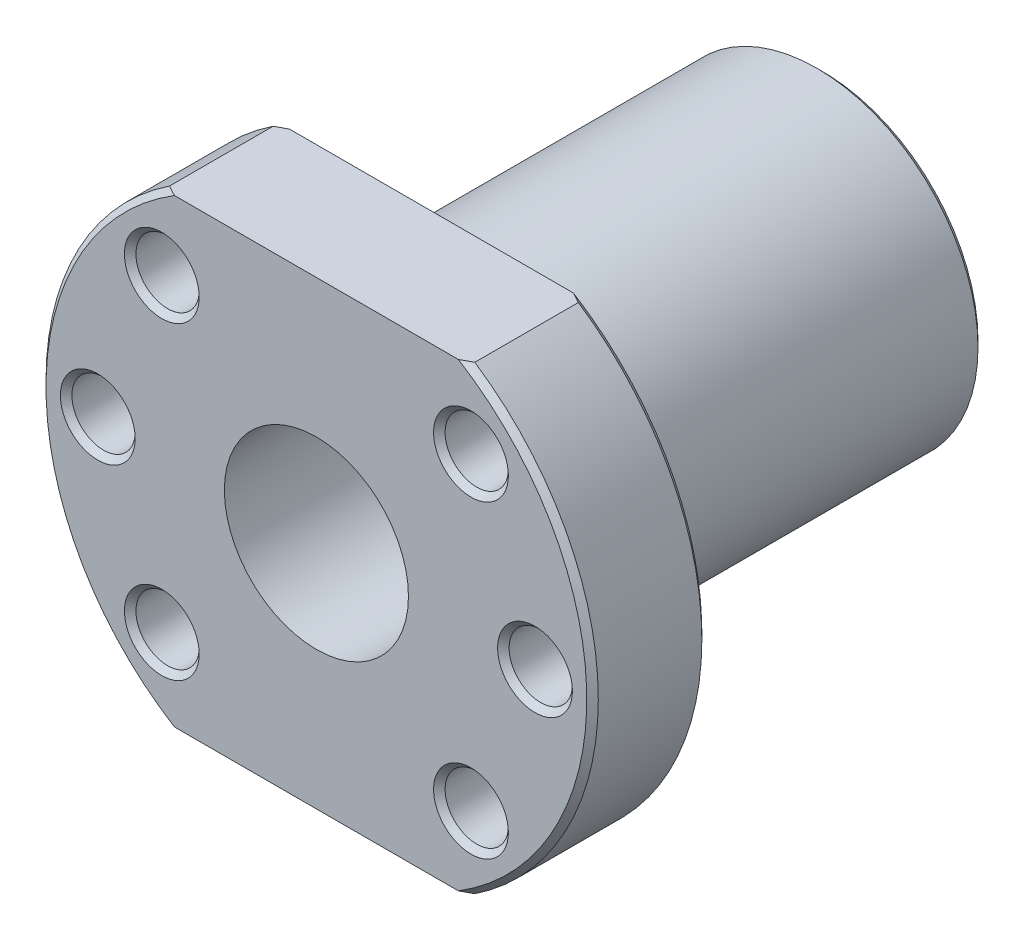
SolidWorks part; units mm, degrees
ref_plane "Front Plane" through (0, 0, 0) normal (0, 0, 1) x (1, 0, 0)
ref_plane "Top Plane" through (0, 0, 0) normal (0, 1, 0) x (1, 0, 0)
ref_plane "Right Plane" through (0, 0, 0) normal (1, 0, 0) x (0, 0, -1)
sketch "Sketch1" plane through (0, 0, 0) normal (0, 0, 1) x (1, 0, 0)
  circle A0 centre (0, 0) radius 24
  dimension "D1" = 48
extrude "Boss-Extrude1" add sketch "Sketch1" along normal blind 10
sketch "Sketch2" plane through (0, 0, 0) normal (0, 0, -1) x (-1, 0, 0)
  circle A0 centre (0, 0) radius 14
  dimension "D1" = 28
extrude "Boss-Extrude2" add sketch "Sketch2" along normal blind 34
sketch "Sketch3" plane through (0, 0, 10) normal (0, 0, 1) x (1, 0, 0)
  line L1 (-44.2312, 43.5302) -> (38.4533, 43.5302)
  line L2 (-44.2312, 43.5302) -> (-44.2312, 20)
  line L3 (-44.2312, 20) -> (38.4533, 20)
  line L4 (38.4533, 43.5302) -> (38.4533, 20)
  line L5 (-33.773, -43.293) -> (38.4533, -43.293)
  line L6 (-33.773, -43.293) -> (-33.773, -20)
  line L7 (-33.773, -20) -> (38.4533, -20)
  line L8 (38.4533, -43.293) -> (38.4533, -20)
  circle A0 centre (0, 0) radius 24 construction
  dimension "D1" = 82.6844
  dimension "D2" = 72.2263
  dimension "D3" = 20
  dimension "D4" = 20
extrude "Cut-Extrude1" cut sketch "Sketch3" against normal up to next
sketch "Sketch4" plane through (0, 0, -34) normal (0, 0, -1) x (-1, 0, 0)
  circle A0 centre (0, 0) radius 8
  dimension "D1" = 16
extrude "Cut-Extrude2" cut sketch "Sketch4" against normal up to next
sketch "Sketch7" plane through (0, 0, 10) normal (0, 0, 1) x (1, 0, 0)
  line L0 (0, 0) -> (0, 27.0897) construction
  line L1 (0, 0) -> (-25.3091, 25.3091) construction
  line L2 (0, 0) -> (-38, 0) construction
  line L3 (0, 0) -> (-1.1117, -1.1117) construction
  line L4 (0, 0) -> (-22.119, -22.119) construction
  circle A0 centre (-13.435, 13.435) radius 2.75
  circle A1 centre (-19, 0) radius 2.75
  circle A2 centre (-13.435, -13.435) radius 2.75
  dimension "D1" = 5.5
  dimension "D4" = 5.5
  dimension "D7" = 5.5
  dimension "D2" = 45
  dimension "D3" = 19
  dimension "D5" = 19
  dimension "D6" = 45
  dimension "D8" = 19
extrude "Cut-Extrude3" cut sketch "Sketch7" against normal up to next (10 mm away)
chamfer "Chamfer1" distance 0.5 angle 45 3 edges at (-10.685, -13.435, 10) (-16.25, 0, 10) (-10.685, 13.435, 10)
mirror "Mirror1" about plane through (0, 0, 0) normal (1, 0, 0) of "Chamfer1", "Cut-Extrude3"
chamfer "Chamfer2" distance 0.5 angle 45 5 edges at (-14, 0, -34) (24, 0, 0) (-24, 0, 0) (24, 0, 10) (-24, 0, 10)
